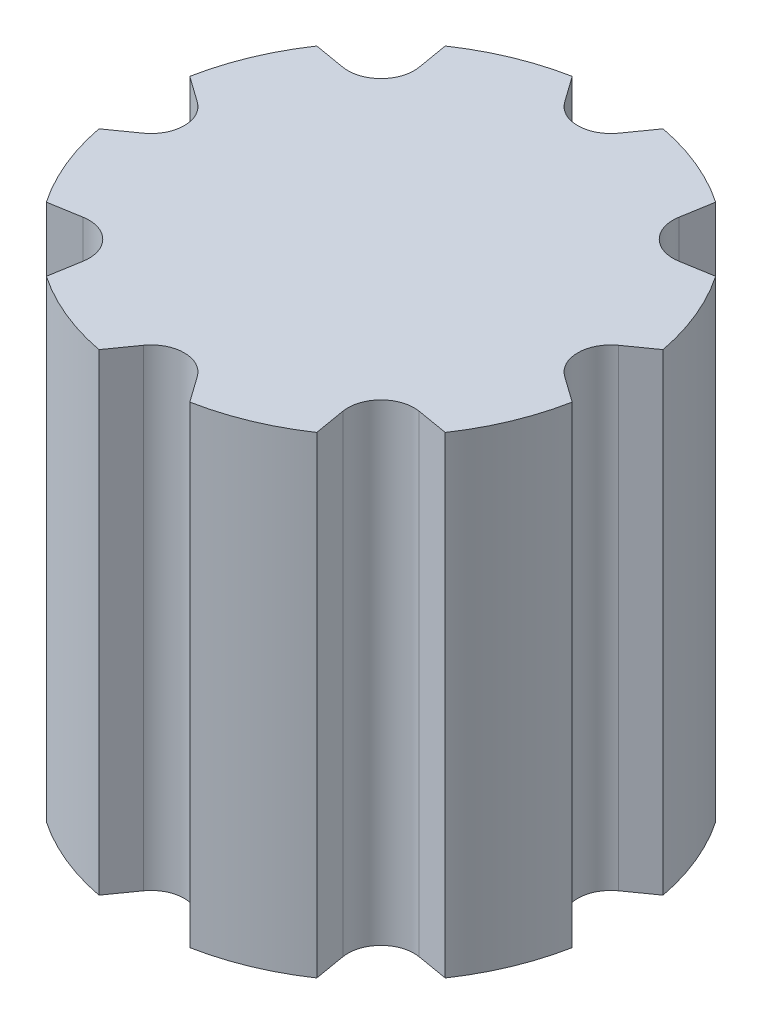
SolidWorks part; units mm, degrees
ref_plane "Front" through (0, 0, 0) normal (0, 0, 1) x (1, 0, 0)
ref_plane "Top" through (0, 0, 0) normal (0, 1, 0) x (1, 0, 0)
ref_plane "Right" through (0, 0, 0) normal (1, 0, 0) x (0, 0, -1)
sketch "Sketch1" plane through (0, 0, 0) normal (0, 1, 0) x (1, 0, 0)
  line L0 (-1, 5.4083) -> (-0.4077, 4.5741)
  line L1 (0.4077, 4.5741) -> (1, 5.4083)
  line L2 (3.5227, 2.9461) -> (4.5314, 3.1172)
  line L3 (3.1172, 4.5314) -> (2.9461, 3.5227)
  line L4 (4.5741, -0.4077) -> (5.4083, -1)
  line L5 (5.4083, 1) -> (4.5741, 0.4077)
  line L6 (2.9461, -3.5227) -> (3.1172, -4.5314)
  line L7 (4.5314, -3.1172) -> (3.5227, -2.9461)
  line L8 (-0.4077, -4.5741) -> (-1, -5.4083)
  line L9 (1, -5.4083) -> (0.4077, -4.5741)
  line L10 (-3.5227, -2.9461) -> (-4.5314, -3.1172)
  line L11 (-3.1172, -4.5314) -> (-2.9461, -3.5227)
  line L12 (-4.5741, 0.4077) -> (-5.4083, 1)
  line L13 (-5.4083, -1) -> (-4.5741, -0.4077)
  line L14 (-2.9461, 3.5227) -> (-3.1172, 4.5314)
  line L15 (-4.5314, 3.1172) -> (-3.5227, 2.9461)
  line L16 (-4.5648, 2.92) -> (-3.5561, 2.749)
  line L17 (-2.749, 3.5561) -> (-2.92, 4.5648)
  line L18 (-1.1631, 5.2925) -> (-0.5708, 4.4584)
  line L19 (0.5708, 4.4584) -> (1.1631, 5.2925)
  line L20 (2.92, 4.5648) -> (2.749, 3.5561)
  line L21 (3.5561, 2.749) -> (4.5648, 2.92)
  line L22 (5.2925, 1.1631) -> (4.4584, 0.5708)
  line L23 (4.4584, -0.5708) -> (5.2925, -1.1631)
  line L24 (4.5648, -2.92) -> (3.5561, -2.749)
  line L25 (2.749, -3.5561) -> (2.92, -4.5648)
  line L26 (1.1631, -5.2925) -> (0.5708, -4.4584)
  line L27 (-0.5708, -4.4584) -> (-1.1631, -5.2925)
  line L28 (-2.92, -4.5648) -> (-2.749, -3.5561)
  line L29 (-3.5561, -2.749) -> (-4.5648, -2.92)
  line L30 (-5.2925, -1.1631) -> (-4.4584, -0.5708)
  line L31 (-4.4584, 0.5708) -> (-5.2925, 1.1631)
  circle A0 centre (0, 0) radius 5.5
  arc A1 (-0.4077, 4.5741) -> (0.4077, 4.5741) centre (0, 4.8636) ccw
  arc A2 (2.9461, 3.5227) -> (3.5227, 2.9461) centre (3.4391, 3.4391) ccw
  arc A3 (4.5741, 0.4077) -> (4.5741, -0.4077) centre (4.8636, 0) ccw
  arc A4 (3.5227, -2.9461) -> (2.9461, -3.5227) centre (3.4391, -3.4391) ccw
  arc A5 (0.4077, -4.5741) -> (-0.4077, -4.5741) centre (0, -4.8636) ccw
  arc A6 (-2.9461, -3.5227) -> (-3.5227, -2.9461) centre (-3.4391, -3.4391) ccw
  arc A7 (-4.5741, -0.4077) -> (-4.5741, 0.4077) centre (-4.8636, 0) ccw
  arc A8 (-3.5227, 2.9461) -> (-2.9461, 3.5227) centre (-3.4391, 3.4391) ccw
  circle A9 centre (0, 0) radius 5.1
  arc A10 (-3.5561, 2.749) -> (-2.749, 3.5561) centre (-3.4391, 3.4391) ccw
  arc A11 (-0.5708, 4.4584) -> (0.5708, 4.4584) centre (0, 4.8636) ccw
  arc A12 (2.749, 3.5561) -> (3.5561, 2.749) centre (3.4391, 3.4391) ccw
  arc A13 (4.4584, 0.5708) -> (4.4584, -0.5708) centre (4.8636, 0) ccw
  arc A14 (3.5561, -2.749) -> (2.749, -3.5561) centre (3.4391, -3.4391) ccw
  arc A15 (0.5708, -4.4584) -> (-0.5708, -4.4584) centre (0, -4.8636) ccw
  arc A16 (-2.749, -3.5561) -> (-3.5561, -2.749) centre (-3.4391, -3.4391) ccw
  arc A17 (-4.4584, -0.5708) -> (-4.4584, 0.5708) centre (-4.8636, 0) ccw
  point P10 (0, 4)
  point P46 (0, 0)
  dimension "D1" = 11
  dimension "D4" = 0.5
  dimension "D6" = 0.4
  dimension "D2" = 4
  dimension "D3" = 2
  dimension "D7" = 0.2
  dimension "D5" = 8
extrude "Boss-Extrude1" add sketch "Sketch1" along normal blind 10 contours A17 L30 A9 L29 A16 L28 L27 A15 L26 L25 A14 L24 L23 A13 L22 L21 A12 L20 L19 A11 L18 L17 A10 L16 L31
sketch "Sketch2" plane through (0, 0, 0) normal (0, -1, 0) x (1, 0, 0)
  circle A0 centre (0, 0) radius 1.5
  dimension "D1" = 3
extrude "Cut-Extrude1" cut sketch "Sketch2" against normal blind 5
